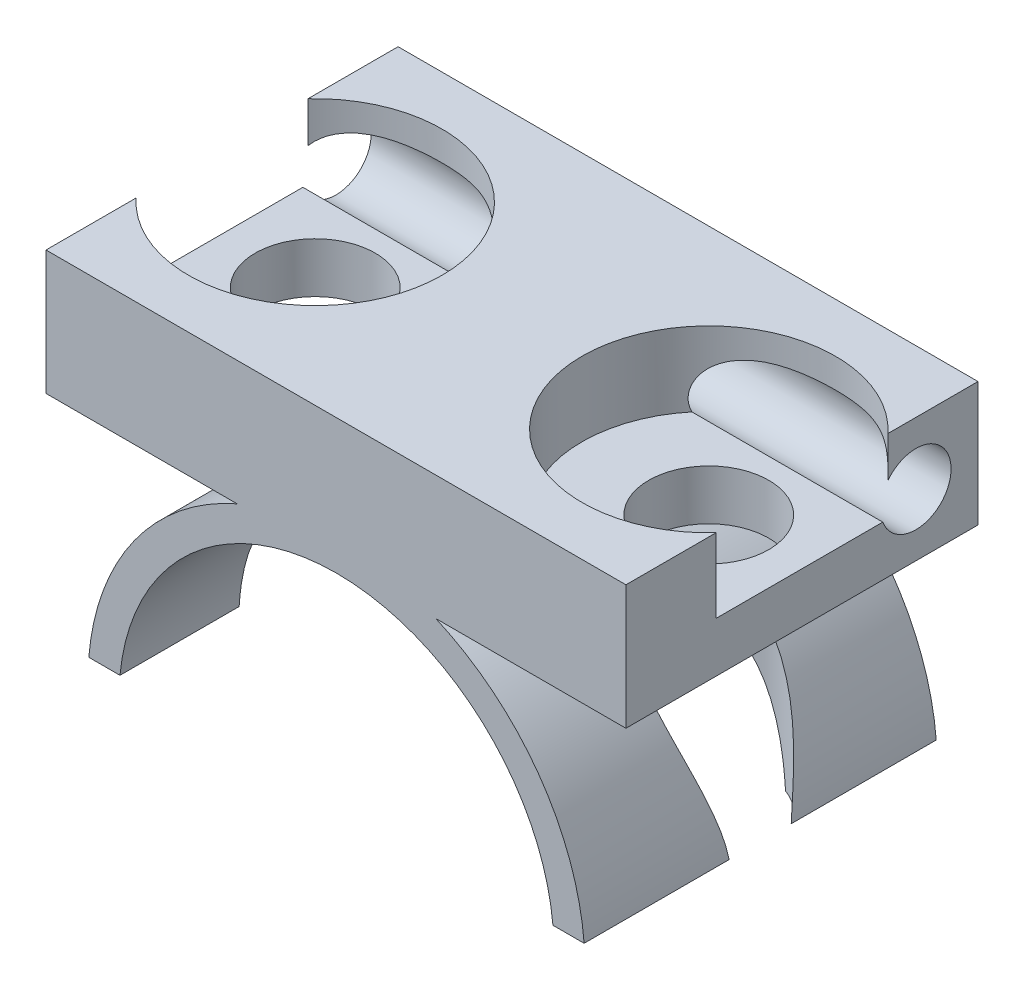
SolidWorks part; units mm, degrees
ref_plane "Alzado" through (0, 0, 0) normal (0, 0, 1) x (1, 0, 0)
ref_plane "Planta" through (0, 0, 0) normal (0, 1, 0) x (1, 0, 0)
ref_plane "Vista lateral" through (0, 0, 0) normal (1, 0, 0) x (0, 0, -1)
sketch "Croquis1" plane through (0, 0, 0) normal (0, 0, 1) x (1, 0, 0)
  line L1 (13.9755, 17) -> (-14.0245, 17)
  line L2 (13.9755, 17) -> (13.9755, 11)
  line L3 (13.9755, 11) -> (-14.0245, 11)
  line L4 (-14.0245, 17) -> (-14.0245, 11)
  line L5 (13.9755, 17) -> (-14.0245, 11) construction
  line L6 (13.9755, 11) -> (-14.0245, 17) construction
  line L22 (18.2279, 1) -> (-22.6663, 1)
  circle A0 centre (0, 0) radius 10.5
  circle A1 centre (0, 0) radius 12
  point P4 (-0.0245, 14)
  dimension "D1" = 21
  dimension "D2" = 24
  dimension "D3" = 6
  dimension "D4" = 28
  dimension "D5" = 13
  dimension "D6" = 14
extrude "Saliente-Extruir1" add sketch "Croquis1" along normal blind 17 contours L3 A1 A0 | A1 L3 L2 L1 L4 | L3 A1
sketch "Croquis4" plane through (13.9755, 0, 0) normal (1, 0, 0) x (0, 0, -1)
  point P0 (-3, 14)
hole_wizard "Taladro de margen para M31" positions "Croquis7" profile "Croquis6" hole size "M3" standard "Ansi Metric" end condition through all
sketch "Croquis7" plane through (13.9755, 0, 0) normal (1, 0, 0) x (0, 0, -1)
  point P0 (-3, 14)
sketch "Croquis6" plane through (13.9755, 14, 3) normal (0, 1, 0) x (0, 0, -1)
  line L0 (0, 0) -> (0, 28)
  line L1 (0, 28) -> (1.7, 28)
  line L2 (1.7, 28) -> (1.7, 0)
  line L5 (1.7, 0) -> (0, 0)
  line L11 (0, -6.35) -> (0, 107.95) construction
  dimension "Diámetro de taladro hasta el siguiente" = 3.4
  dimension "Profundidad de taladro hasta el siguiente" = 28
hole_wizard "Refrentado para perno con cabeza hexagonal de M51" positions "Croquis12" profile "Croquis13" counterbore size "M5" standard "Ansi Metric" end condition through all
sketch "Croquis12" plane through (0, 17, 0) normal (0, 1, 0) x (1, 0, 0)
  line L0 (-14.0245, -8.5) -> (13.9755, -8.5)
  line L1 (-14.0245, -17) -> (-14.0245, 0) construction
  line L2 (13.9755, -17) -> (13.9755, 0) construction
  point P8 (-9.5245, -8.5)
  point P10 (9.4755, -8.5)
  dimension "D1" = 19
  dimension "D2" = 4.5
sketch "Croquis13" plane through (9.4755, 17, 8.5) normal (1, 0, 0) x (0, 0, 1)
  line L0 (0, 0) -> (0, 16)
  line L1 (0, 16) -> (2.9, 16)
  line L3 (2.9, 16) -> (2.9, 3.58)
  line L4 (2.9, 3.58) -> (6.12, 3.58)
  line L5 (6.12, 3.58) -> (6.12, 0)
  line L7 (6.12, 0) -> (0, 0)
  line L11 (0, -6.35) -> (0, 107.95) construction
  dimension "Diámetro de taladro hasta el siguiente" = 5.8
  dimension "Profundidad de taladro hasta el siguiente" = 16
  dimension "Diámetro de refrentado" = 12.24
  dimension "Profundidad de refrentado" = 3.58
